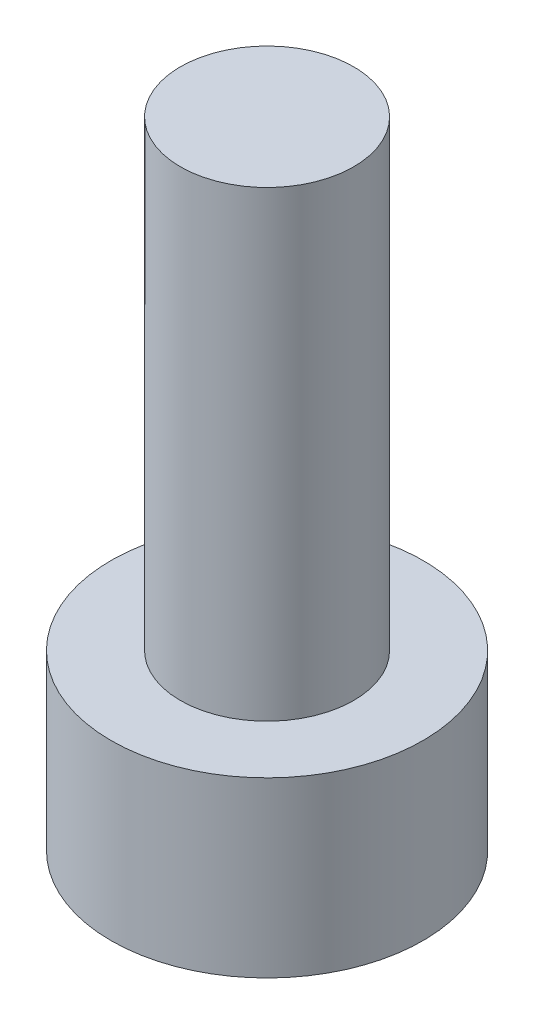
SolidWorks part; units mm, degrees
ref_plane "Front" through (0, 0, 0) normal (0, 0, 1) x (1, 0, 0)
ref_plane "Top" through (0, 0, 0) normal (0, 1, 0) x (1, 0, 0)
ref_plane "Right" through (0, 0, 0) normal (1, 0, 0) x (0, 0, -1)
sketch "Sketch1" plane through (0, 0, 0) normal (0, 1, 0) x (1, 0, 0)
  circle A0 centre (0, 0) radius 2.7
  dimension "D1" = 5.4
extrude "Boss-Extrude1" add sketch "Sketch1" along normal blind 3
sketch "Sketch2" plane through (0, 3, 0) normal (0, 1, 0) x (1, 0, 0)
  circle A0 centre (0, 0) radius 1.5
  circle A1 centre (0, 0) radius 2.7
  circle A2 centre (0, 0) radius 2.7
  dimension "D2" = 3
  dimension "D1" = 0
extrude "Boss-Extrude2" add sketch "Sketch2" along normal blind 8 contours A0
